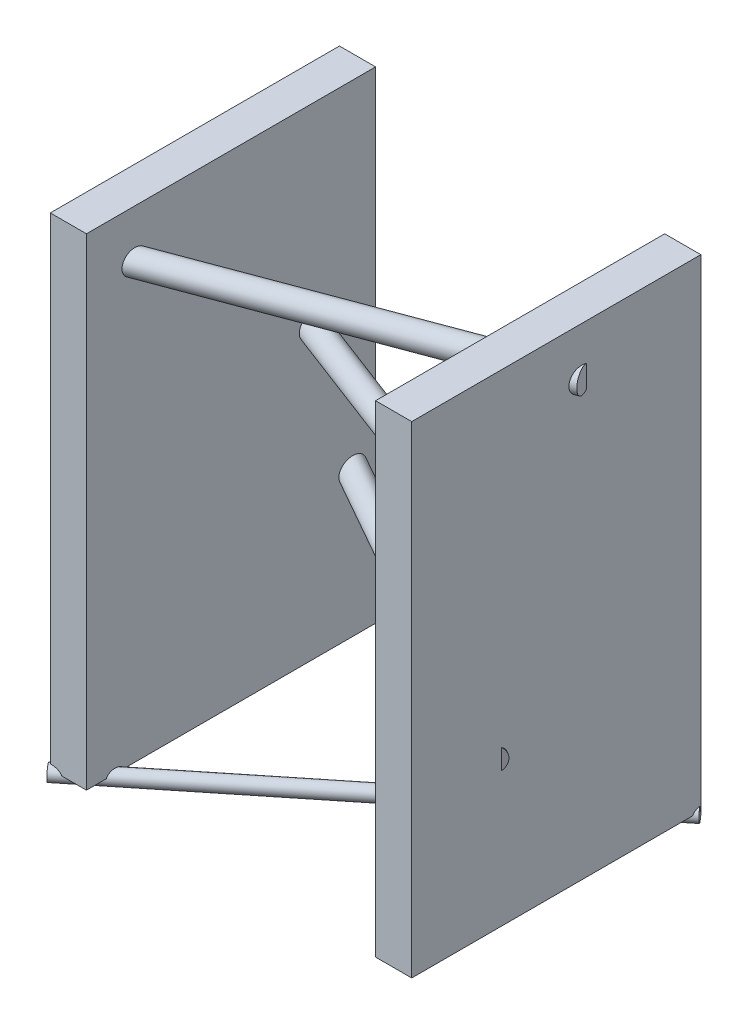
SolidWorks part; units mm, degrees
ref_plane "正面" through (0, 0, 0) normal (0, 0, 1) x (1, 0, 0)
ref_plane "平面" through (0, 0, 0) normal (0, 1, 0) x (1, 0, 0)
ref_plane "右側面" through (0, 0, 0) normal (1, 0, 0) x (0, 0, -1)
sketch "ｽｹｯﾁ1" plane through (0, 0, 0) normal (0, 0, 1) x (1, 0, 0)
  line L1 (750, -1000) -> (-750, -1000)
  line L2 (750, -1000) -> (750, 1000)
  line L3 (750, 1000) -> (-750, 1000)
  line L4 (-750, -1000) -> (-750, 1000)
  line L5 (750, -1000) -> (-750, 1000) construction
  line L6 (750, 1000) -> (-750, -1000) construction
  point P0 (0, 0)
  dimension "D1" = 1500
  dimension "D2" = 2000
extrude "ﾎﾞｽ - 押し出し1" add sketch "ｽｹｯﾁ1" along normal blind 1200
sketch "ｽｹｯﾁ2" plane through (0, -1000, 0) normal (0, -1, 0) x (1, 0, 0)
  line L0 (-750, 0) -> (750, 0) construction
  line L1 (-600, 0) -> (600, 0)
  line L2 (-600, 0) -> (-600, 1200)
  line L3 (-600, 1200) -> (600, 1200)
  line L4 (600, 0) -> (600, 1200)
  line L5 (-750, 1200) -> (750, 1200) construction
  dimension "D1" = 150
  dimension "D2" = 1200
extrude "ｶｯﾄ - 押し出し1" cut sketch "ｽｹｯﾁ2" against normal blind 2000
sketch "ｽｹｯﾁ3" plane through (750, 0, 0) normal (1, 0, 0) x (0, 0, -1)
  line L0 (-1200, -1000) -> (-1200, 600)
  line L1 (-1200, -1000) -> (-1200, 1000) construction
  line L2 (-1200, 600) -> (-342.2892, -1000)
  line L3 (-1200, -1000) -> (0, -1000) construction
  line L4 (-342.2892, -1000) -> (-1200, -1000)
  dimension "D1" = 1600
sketch3d "3Dｽｹｯﾁ1" plane through (0, 0, 0) normal (0, 0, 1) x (1, 0, 0)
  dimension "D1" = 10
  dimension "D2" = 600
  dimension "D3" = 1200
  dimension "D4" = 1800
sketch "ｽｹｯﾁ5" plane through (0, -1010, 0) normal (0, -1, 0) x (-1, 0, 0)
  line L0 (-746.5099, 0) -> (754.1697, -1205.3767)
sketch "ｽｹｯﾁ6" plane through (0, -400, 0) normal (0, -1, 0) x (-1, 0, 0)
  line L0 (-736.3273, -851.0946) -> (767.8891, 0)
sketch3d "3Dｽｹｯﾁ2"
  point P0 (693.9706, -1000, 768.2389)
sweep "ｽｲｰﾌﾟ1" add path "ｽｹｯﾁ5" circular profile diameter 60 parameters "D3"=60
sweep "ｽｲｰﾌﾟ2" add path "ｽｹｯﾁ6" circular profile diameter 100 parameters "D3"=100
sketch "ｽｹｯﾁ35" plane through (0, 800, 0) normal (0, -1, 0) x (-1, 0, 0)
  line L0 (-756.2037, -491.8498) -> (758.5708, -1058.3834)
  point P2 (-756.2037, -491.8498)
sweep "ｽｲｰﾌﾟ3" add path "ｽｹｯﾁ35" circular profile diameter 100 parameters "D3"=100
sketch "ｽｹｯﾁ50" plane through (0, 200, 0) normal (0, -1, 0) x (-1, 0, 0)
  line L0 (-726.4191, -768.6807) -> (692.0238, -228.1293)
sweep "ｽｲｰﾌﾟ4" add path "ｽｹｯﾁ50" circular profile diameter 100 parameters "D3"=100
